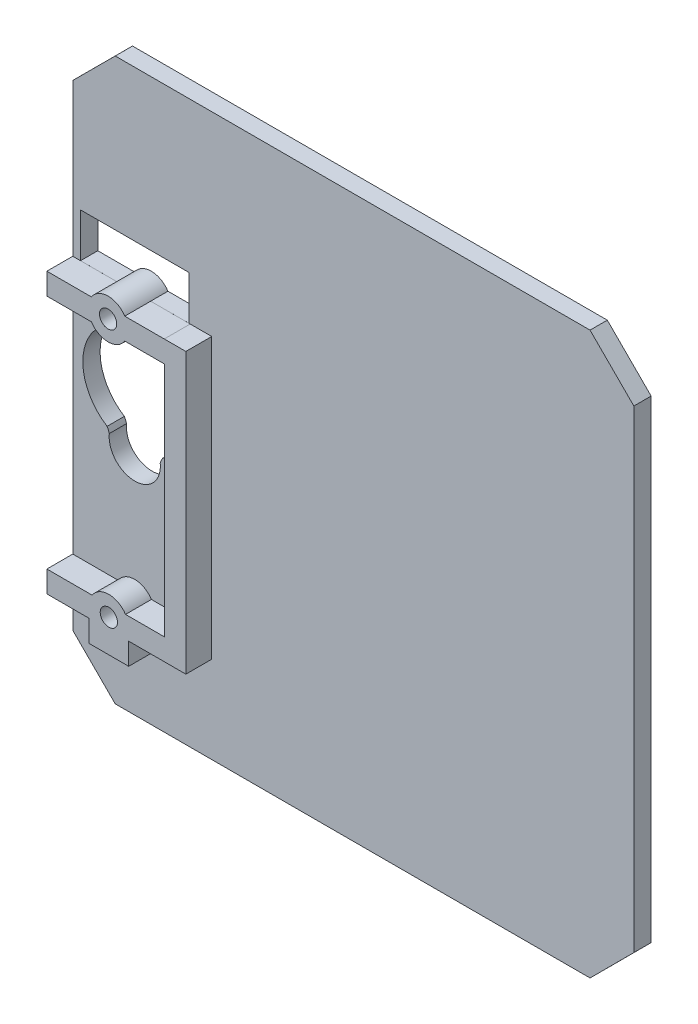
SolidWorks part; units mm, degrees
ref_plane "Front Plane" through (0, 0, 0) normal (0, 0, 1) x (1, 0, 0)
ref_plane "Top Plane" through (0, 0, 0) normal (0, 1, 0) x (1, 0, 0)
ref_plane "Right Plane" through (0, 0, 0) normal (1, 0, 0) x (0, 0, -1)
sketch "Sketch2" plane through (0, 0, 0) normal (0, 0, 1) x (1, 0, 0)
  line L0 (7.0704, 67) -> (62.0787, 67)
  line L1 (5.0821, 0) -> (64.0909, 0)
  line L2 (0.1535, 4.9273) -> (0.1535, 64.0678)
  line L3 (5.0821, 69) -> (64.0909, 69)
  line L4 (69.1535, 5.0681) -> (69.1535, 63.9268)
  line L6 (2.1535, 62.0879) -> (2.1535, 6.9169)
  line L7 (7.0704, 2) -> (62.0787, 2)
  line L8 (67.1535, 61.9216) -> (67.1535, 7.0833)
  line L9 (9.2454, 44.45) -> (9.2454, 43.1985) construction
  line L10 (3.0535, 49.55) -> (15.6035, 49.55)
  line L11 (3.0535, 49.55) -> (3.0535, 44.45)
  line L12 (0, 70.9946) -> (4.9989, 70.9946) construction
  line L13 (3.0535, 44.45) -> (7.3157, 44.45)
  line L14 (15.6035, 49.55) -> (15.6035, 44.45)
  line L15 (18.1456, 44.4709) -> (18.1456, 12.0709)
  line L16 (0.1535, 64.0678) -> (5.0821, 69)
  line L17 (2.1535, 62.0879) -> (7.0704, 67)
  line L19 (10.2504, 13.3209) -> (10.5004, 13.3209)
  line L20 (0.1535, 4.9273) -> (5.0821, 0)
  line L21 (2.1535, 6.9169) -> (7.0704, 2)
  line L22 (15.6456, 44.4709) -> (18.1456, 44.4709)
  line L23 (15.7505, 41.9485) -> (15.7505, 14.5709)
  line L26 (2.1535, 14.5709) -> (7.486, 14.5709)
  line L28 (69.1535, 5.0681) -> (64.0909, 0)
  line L29 (67.1535, 7.0833) -> (62.0787, 2)
  line L30 (64.0909, 69) -> (69.1535, 63.9268)
  line L31 (62.0787, 67) -> (67.1535, 61.9216)
  line L32 (2.0704, 12.0709) -> (7.486, 12.0709)
  line L34 (2.1535, 44.4485) -> (7.3147, 44.4485)
  line L36 (2.0704, 41.9485) -> (7.3147, 41.9485)
  line L38 (8.0835, 11.4734) -> (8.0835, 8.6259)
  line L39 (8.0835, 8.6259) -> (10.5835, 8.6259)
  line L40 (10.5835, 11.4734) -> (10.5835, 8.6259)
  line L41 (11.1811, 14.5709) -> (15.7505, 14.5709)
  line L42 (11.1811, 12.0709) -> (18.1456, 12.0709)
  line L43 (11.1751, 44.45) -> (15.6035, 44.45)
  line L44 (11.1761, 44.4485) -> (17.3391, 44.4485)
  line L45 (11.1761, 41.9485) -> (15.7505, 41.9485)
  circle A0 centre (9.2454, 43.1985) radius 2.3
  arc A1 (12.5614, 29.3869) -> (6.1286, 29.3724) centre (9.3335, 34.4637) ccw
  arc A2 (6.385, 28.7755) -> (12.2823, 28.7732) centre (9.3335, 28.4476) ccw
  arc A3 (12.5614, 29.3869) -> (12.2823, 28.7732) centre (15.2238, 27.8058) ccw
  arc A4 (6.1286, 29.3724) -> (6.385, 28.7755) centre (3.4671, 27.8755) cw
  circle A5 centre (9.2454, 43.1985) radius 1
  circle A6 centre (9.3335, 13.3209) radius 2.2307
  circle A7 centre (9.3335, 13.3209) radius 0.9169
  dimension "D9" = 7.18
  dimension "D11" = 53.6791
  dimension "D12" = 7.18
  dimension "D13" = 6.417
  dimension "D1" = 12.55
  dimension "D2" = 5.1
  dimension "D3" = 2
  dimension "D4" = 2
  dimension "D5" = 2
  dimension "D6" = 0.9
  dimension "D7" = 17.45
  dimension "D8" = 1.2515
  dimension "D10" = 32.5363
  dimension "D14" = 2.5
  dimension "D15" = 2.5
  dimension "D16" = 1.25
  dimension "D18" = 1.25
  dimension "D19" = 1.25
extrude "Boss-Extrude3" add sketch "Sketch2" along normal blind 2
sketch "Sketch7" plane through (0, 0, 2) normal (0, 0, 1) x (1, 0, 0)
  line L0 (2.1535, 62.0879) -> (2.1535, 6.9169) construction
  line L1 (7.0704, 67) -> (62.0787, 67) construction
  line L2 (11.2642, 14.57) -> (18.2535, 14.57)
  line L3 (15.7535, 44.45) -> (18.2535, 44.45)
  line L4 (15.7535, 44.45) -> (15.7535, 44.4485)
  line L6 (18.2535, 44.45) -> (18.2535, 16.5346)
  line L7 (2.1535, 44.4485) -> (7.3147, 44.4485)
  line L8 (2.1535, 44.4485) -> (2.1535, 41.9485)
  line L9 (2.1535, 41.9485) -> (7.3147, 41.9485)
  line L11 (2.1535, 14.57) -> (7.4028, 14.57)
  line L12 (2.1535, 14.57) -> (2.1535, 12.07)
  line L13 (2.1535, 12.07) -> (7.4028, 12.07)
  line L14 (18.2535, 14.57) -> (18.2535, 12.07)
  line L16 (15.7535, 16.5346) -> (15.7535, 12.07)
  line L17 (15.7535, 12.07) -> (18.2535, 12.07)
  line L18 (18.2535, 16.5346) -> (18.2535, 12.07)
  line L20 (7.0335, 12.07) -> (7.0335, 9.5478)
  line L21 (7.0335, 9.5478) -> (11.6335, 9.5478)
  line L22 (11.6335, 12.07) -> (11.6335, 9.5478)
  line L23 (11.2642, 12.07) -> (18.2535, 12.07)
  line L24 (15.7535, 41.9485) -> (15.7535, 16.5346)
  line L25 (11.1761, 44.4485) -> (17.3319, 44.4485)
  line L26 (11.1761, 41.9485) -> (15.7535, 41.9485)
  arc A0 (7.3157, 44.45) -> (7.3147, 44.4485) centre (9.2454, 43.1985) ccw
  arc A1 (11.1751, 44.45) -> (7.3157, 44.45) centre (9.2454, 43.1985) ccw construction
  circle A2 centre (9.2454, 43.1985) radius 1
  arc A3 (11.2642, 14.57) -> (7.4028, 14.57) centre (9.3335, 13.32) ccw
  circle A4 centre (9.3335, 13.32) radius 1
  arc A5 (3.3174, 34.4637) -> (9.3199, 40.4798) centre (9.3335, 34.4637) ccw
  arc A6 (12.5614, 29.3869) -> (6.1286, 29.3724) centre (9.3335, 34.4637) ccw construction
  arc A7 (7.3147, 41.9485) -> (11.1761, 41.9485) centre (9.2454, 43.1985) ccw
  arc A8 (11.1761, 44.4485) -> (9.2454, 45.4985) centre (9.2454, 43.1985) ccw
  arc A9 (7.4028, 12.07) -> (11.2642, 12.07) centre (9.3335, 13.32) ccw
  dimension "D1" = 7.18
  dimension "D3" = 6.42
  dimension "D2" = 53.68
  dimension "D4" = 2.5
  dimension "D6" = 1.25
  dimension "D7" = 2.5
  dimension "D8" = 1.25
extrude "Boss-Extrude5" add sketch "Sketch7" along normal blind 3
ref_plane "Plane1" through (34.6535, 0, 0) normal (-1, 0, 0) x (0, 0, 1)
